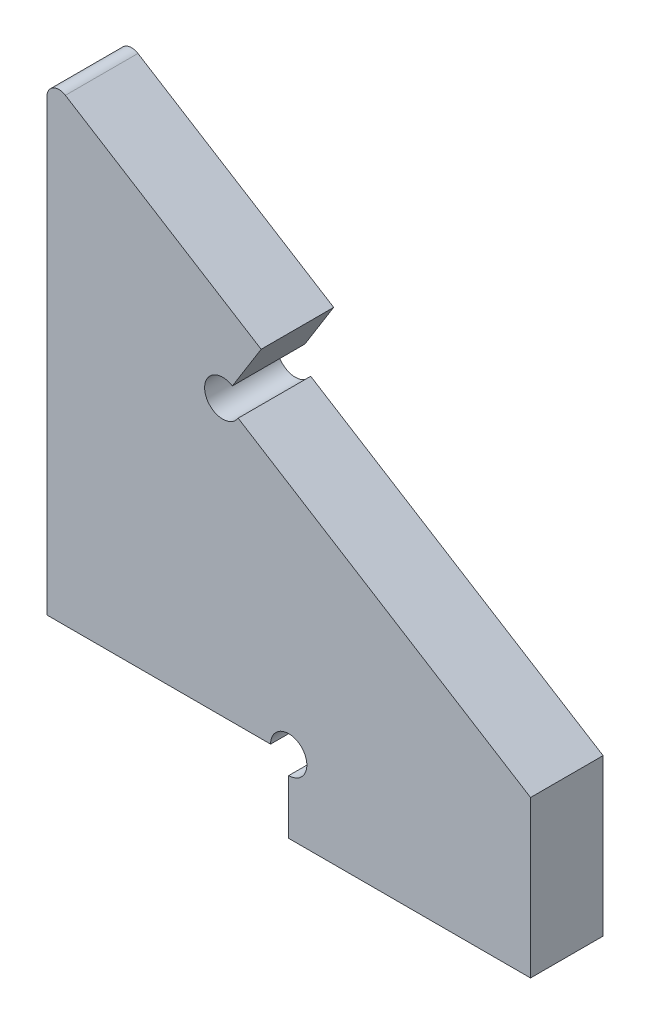
SolidWorks part; units mm, degrees
material "Plain Carbon Steel"
ref_plane "Front Plane" through (0, 0, 0) normal (0, 0, 1) x (1, 0, 0)
ref_plane "Top Plane" through (0, 0, 0) normal (0, 1, 0) x (1, 0, 0)
ref_plane "Right Plane" through (0, 0, 0) normal (1, 0, 0) x (0, 0, -1)
sketch "Sketch1" plane through (0, 0, 0) normal (0, 0, 1) x (1, 0, 0)
  line L0 (711, 120) -> (691, 120)
  line L2 (691, 120) -> (691, 126)
  line L3 (691, 126) -> (711, 126)
  line L4 (711, 126) -> (711, 120)
extrude "Boss-Extrude1" add sketch "Sketch1" along normal blind 6 from surface
sketch "Sketch2" plane through (0, 126, 0) normal (0, 1, 0) x (1, 0, 0)
  line L0 (691, -3) -> (691, 3) construction
  line L1 (671, 3) -> (711, 3)
  line L2 (671, 3) -> (671, -3)
  line L3 (671, -3) -> (711, -3)
  line L4 (711, 3) -> (711, -3)
  line L5 (671, 3) -> (711, -3) construction
  line L6 (671, -3) -> (711, 3) construction
  point P0 (691, 0)
extrude "Boss-Extrude2" add sketch "Sketch2" along normal up to surface (14 mm away)
sketch "Sketch3" plane through (0, 0, 3) normal (0, 0, 1) x (1, 0, 0)
  circle A0 centre (691, 126) radius 1.5
  dimension "D1" = 3
extrude "Cut-Extrude1" cut sketch "Sketch3" against normal through all
fillet "Fillet1" radius 1 1 edges at (671, 164.9414, 0)
sketch "Sketch4" plane through (0, 0, 3) normal (0, 0, 1) x (1, 0, 0)
  line L0 (688.7179, 153.8936) -> (685.5433, 148.8023)
  line L1 (711, 140) -> (672.5291, 163.9879) construction
  line L2 (685.5433, 148.8023) -> (711, 132.9292)
  line L3 (711, 132.9292) -> (714.1746, 138.0205)
  line L4 (688.7179, 153.8936) -> (714.1746, 138.0205)
  line L6 (711, 140) -> (711, 120) construction
  dimension "D1" = 6
  dimension "D2" = 30
extrude "Cut-Extrude3" cut sketch "Sketch4" against normal through all and the other way through all
sketch "Sketch5" plane through (0, 0, 3) normal (0, 0, 1) x (1, 0, 0)
  circle A0 centre (685.5433, 148.8023) radius 1.5
  dimension "D1" = 3
extrude "Cut-Extrude4" cut sketch "Sketch5" against normal through all
